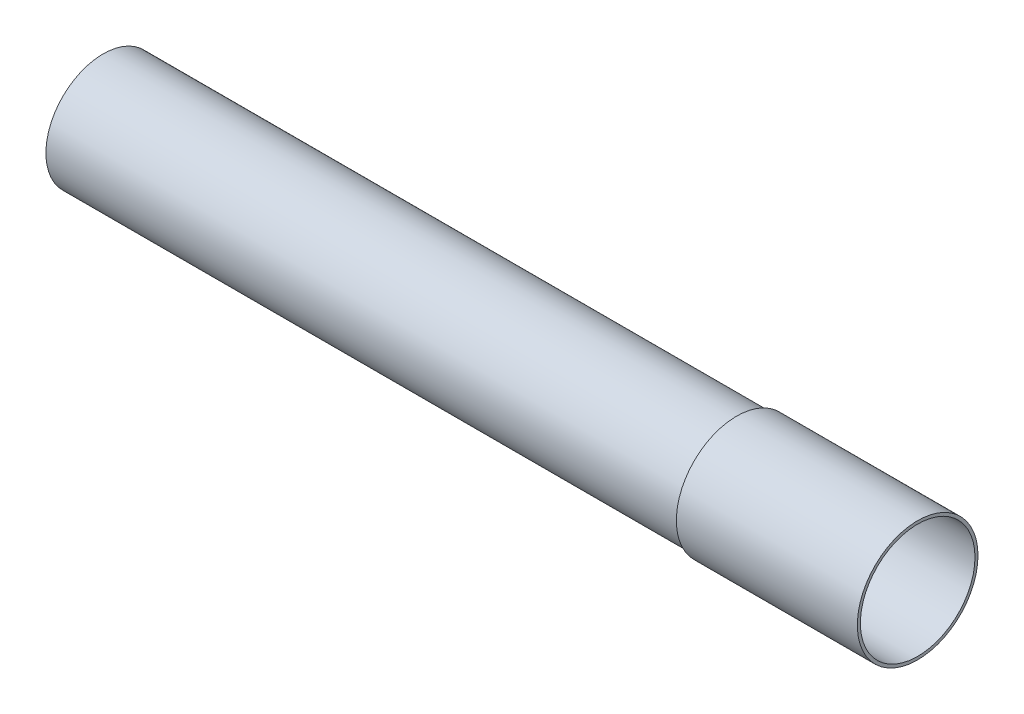
SolidWorks part; units mm, degrees
ref_plane "Front Plane" through (0, 0, 0) normal (0, 0, 1) x (1, 0, 0)
ref_plane "Top Plane" through (0, 0, 0) normal (0, 1, 0) x (1, 0, 0)
ref_plane "Right Plane" through (0, 0, 0) normal (1, 0, 0) x (0, 0, -1)
sketch "Sketch1" plane through (0, 0, 0) normal (1, 0, 0) x (0, 0, -1)
  circle A0 centre (0, 0) radius 19
  circle A1 centre (0, 0) radius 17
  dimension "D1" = 34
  dimension "D2" = 38
extrude "Boss-Extrude1" add sketch "Sketch1" along normal blind 240
sketch "Sketch2" plane through (240, 0, 0) normal (1, 0, 0) x (0, 0, -1)
  circle A0 centre (0, 0) radius 19
  circle A1 centre (0, 0) radius 20
  dimension "D1" = 40
extrude "Boss-Extrude2" add sketch "Sketch2" along normal mid plane 60
